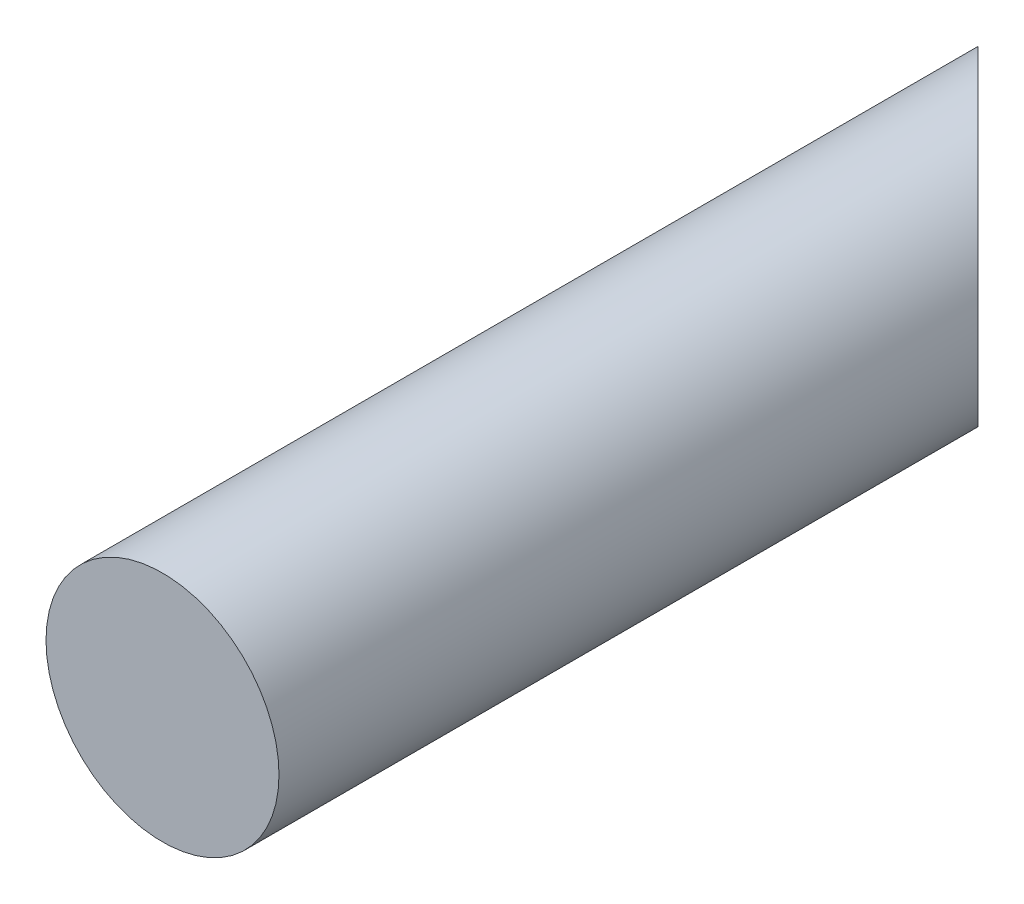
SolidWorks part; units mm, degrees
ref_plane "Front Plane" through (0, 0, 0) normal (0, 0, 1) x (1, 0, 0)
ref_plane "Top Plane" through (0, 0, 0) normal (0, 1, 0) x (1, 0, 0)
ref_plane "Right Plane" through (0, 0, 0) normal (1, 0, 0) x (0, 0, -1)
sketch "Sketch1" plane through (0, 0, 0) normal (0, 0, 1) x (1, 0, 0)
  circle A0 centre (0, 0) radius 30
  dimension "D1" = 60
extrude "Boss-Extrude2" add sketch "Sketch1" along normal blind 240 contours A0
ref_plane "Plane1" through (0, 40, 0) normal (0, 1, 0) x (1, 0, 0)
sketch "Sketch3" plane through (0, 40, 0) normal (0, 1, 0) x (1, 0, 0)
  line L0 (-30, 0) -> (30, -60)
  line L1 (30, -240) -> (30, 0) construction
  line L2 (30, -60) -> (30, 0)
  line L3 (30, 0) -> (-30, 0)
  dimension "D1" = 60
  dimension "D2" = 60
sketch "Sketch4" plane through (0, 40, 0) normal (0, 1, 0) x (1, 0, 0)
  line L0 (-30, -240) -> (30, -240)
  line L1 (30, -240) -> (30, -160)
  line L2 (30, -240) -> (30, 0) construction
  line L3 (30, -160) -> (-30, -240)
  dimension "D1" = 80
extrude "Cut-Extrude1" cut sketch "Sketch3" against normal blind 70
